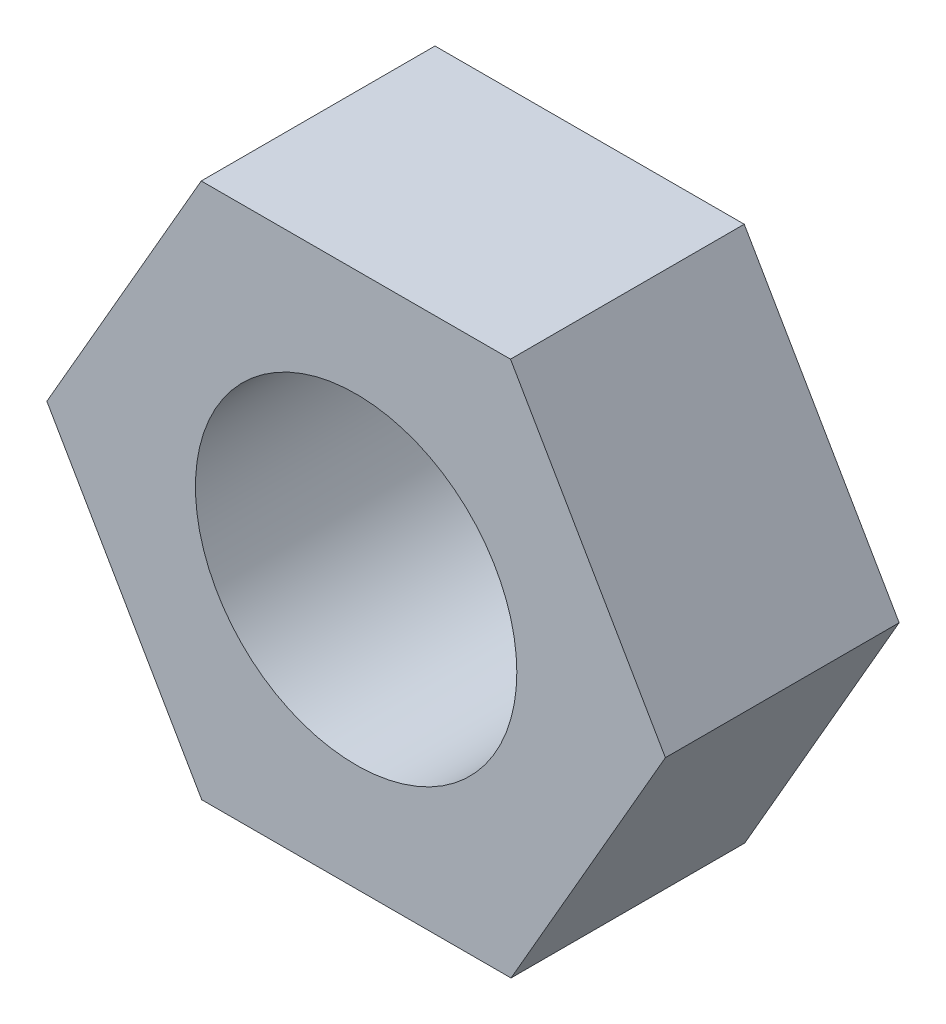
SolidWorks part; units mm, degrees
ref_plane "Přední rovina" through (0, 0, 0) normal (0, 0, 1) x (1, 0, 0)
ref_plane "Horní rovina" through (0, 0, 0) normal (0, 1, 0) x (1, 0, 0)
ref_plane "Pravá rovina" through (0, 0, 0) normal (1, 0, 0) x (0, 0, -1)
sketch "Skica1" plane through (0, 0, 0) normal (0, 0, 1) x (1, 0, 0)
  line L1 (1.585, 2.7515) -> (-1.5904, 2.7485)
  line L2 (-1.5904, 2.7485) -> (-3.1754, -0.0031)
  line L3 (-3.1754, -0.0031) -> (-1.585, -2.7515)
  line L4 (-1.585, -2.7515) -> (1.5904, -2.7485)
  line L5 (1.5904, -2.7485) -> (3.1754, 0.0031)
  line L6 (3.1754, 0.0031) -> (1.585, 2.7515)
  circle A0 centre (0, 0) radius 2.75 construction
  dimension "D1" = 5.5
extrude "Přidat vysunutím1" add sketch "Skica1" along normal blind 2.4
sketch "Skica2" plane through (0, 0, 2.4) normal (0, 0, 1) x (1, 0, 0)
  circle A0 centre (0, 0) radius 1.65
  dimension "D1" = 3.3
extrude "Odebrat vysunutím1" cut sketch "Skica2" against normal blind 2.4
